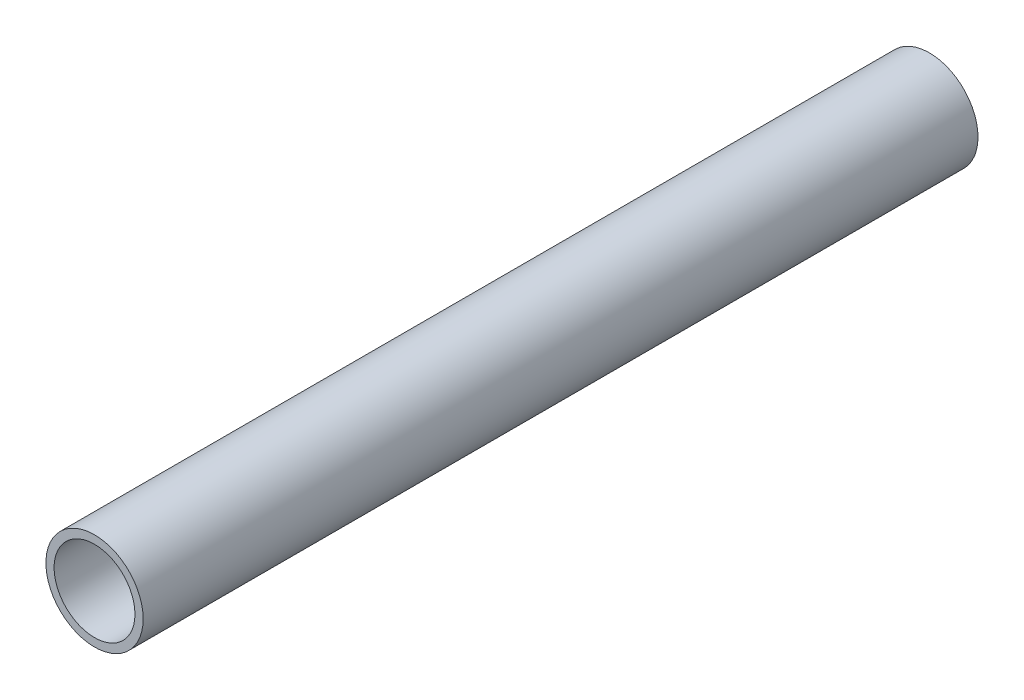
SolidWorks part; units mm, degrees
material "6061 Alloy"
ref_plane "Front Plane" through (0, 0, 0) normal (0, 0, 1) x (1, 0, 0)
ref_plane "Top Plane" through (0, 0, 0) normal (0, 1, 0) x (1, 0, 0)
ref_plane "Right Plane" through (0, 0, 0) normal (1, 0, 0) x (0, 0, -1)
sketch "Sketch1" plane through (0, 0, 0) normal (0, 0, 1) x (1, 0, 0)
  circle A0 centre (0, 0) radius 21.082
  circle A1 centre (0, 0) radius 17.526
  dimension "D1" = 42.164
  dimension "D2" = 35.052
extrude "Boss-Extrude1" add sketch "Sketch1" along normal blind 361.95
